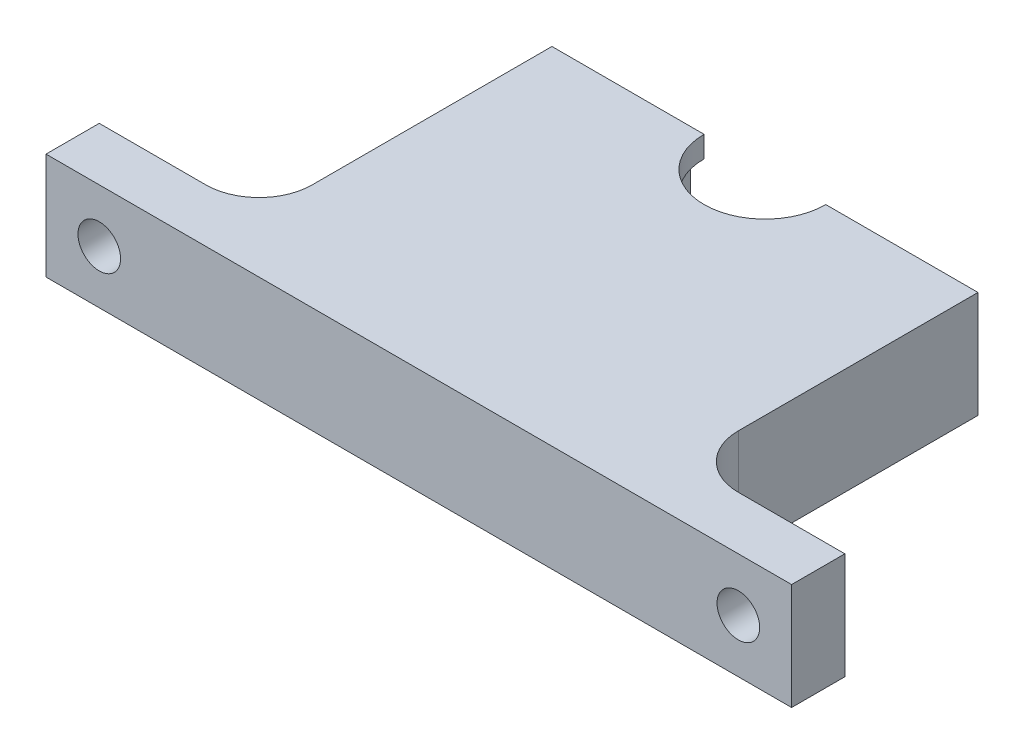
SolidWorks part; units mm, degrees
ref_plane "Front Plane" through (0, 0, 0) normal (0, 0, 1) x (1, 0, 0)
ref_plane "Top Plane" through (0, 0, 0) normal (0, 1, 0) x (1, 0, 0)
ref_plane "Right Plane" through (0, 0, 0) normal (1, 0, 0) x (0, 0, -1)
sketch "Sketch1" plane through (0, 0, 0) normal (0, 1, 0) x (1, 0, 0)
  line L0 (12.7, 0) -> (20, 0)
  line L1 (20, 0) -> (20, -32.5)
  line L2 (20, -32.5) -> (-20, -32.5)
  line L3 (-20, -32.5) -> (-20, 0)
  line L4 (-20, 0) -> (-12.7, 0)
  line L5 (-12.7, 0) -> (12.7, 0)
  circle A0 centre (0, 0) radius 5.715
  arc A1 (12.7, 0) -> (-12.7, 0) centre (0, 0) ccw
  point P8 (0, -32.5)
  dimension "D1" = 11.43
  dimension "D2" = 25.4
  dimension "D3" = 40
  dimension "D4" = 32.5
extrude "main body" add sketch "Sketch1" along normal mid plane 10 contours A0 L5 L4 L3 L2 L1 L0
ref_plane "Plane1" through (0, 0, 0) normal (0, 1, 0) x (1, 0, 0)
sketch "Sketch3" plane through (0, 0, 0) normal (0, 1, 0) x (1, 0, 0)
  circle A0 centre (0, 0) radius 6.985
  dimension "D1" = 13.97
extrude "bearing cutout" cut sketch "Sketch3" against normal mid plane 6
sketch "Sketch4" plane through (0, 0, 0) normal (0, 0, -1) x (-1, 0, 0)
  line L0 (-20, 5) -> (-20, -5) construction
  line L1 (0, -5) -> (0, 5) construction
  line L2 (5.715, 5) -> (-5.715, 5) construction
  circle A0 centre (-15, 0) radius 1.5
  circle A2 centre (15, 0) radius 1.5
  point P5 (-20, 0)
  point P11 (0, 0)
  dimension "D1" = 3
  dimension "D2" = 5
extrude "top mount holes" cut sketch "Sketch4" against normal blind 10
sketch "Sketch6" plane through (0, 0, 32.5) normal (0, 0, 1) x (1, 0, 0)
  line L0 (20, 5) -> (-20, 5) construction
  line L1 (-35, 5) -> (-20, 5)
  line L2 (-35, 5) -> (-35, -5)
  line L3 (-35, -5) -> (-20, -5)
  line L4 (-20, 5) -> (-20, -5)
  line L5 (-35, 5) -> (-20, -5) construction
  line L6 (-35, -5) -> (-20, 5) construction
  line L7 (20, -5) -> (-20, -5) construction
  line L8 (-20, 5) -> (-20, -5) construction
  line L9 (0, -5) -> (0, 5) construction
  line L10 (35, -5) -> (20, -5)
  line L11 (20, 5) -> (20, -5)
  line L12 (35, 5) -> (20, 5)
  line L13 (35, 5) -> (35, -5)
  line L14 (-35, 0) -> (-20, 0) construction
  circle A0 centre (-30, 0) radius 2
  circle A1 centre (30, 0) radius 2
  point P0 (-27.5, 0)
  point P17 (0, 0)
  point P28 (-27.5, 0)
  dimension "D2" = 4
  dimension "D1" = 15
  dimension "D3" = 5
extrude "mounting holes" add sketch "Sketch6" against normal blind 5
fillet "Fillet1" radius 5 2 edges at (20, 0, 27.5) (-20, 0, 27.5)
